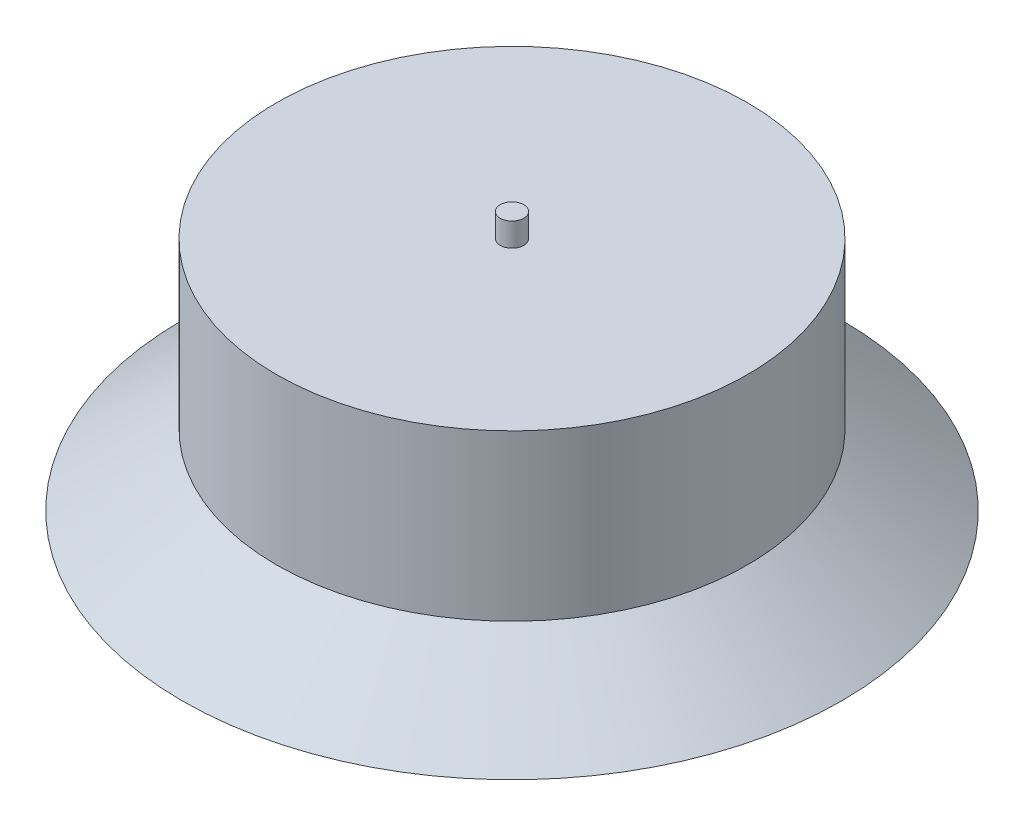
SolidWorks part; units mm, degrees
ref_plane "Front Plane" through (0, 0, 0) normal (0, 0, 1) x (1, 0, 0)
ref_plane "Top Plane" through (0, 0, 0) normal (0, 1, 0) x (1, 0, 0)
ref_plane "Right Plane" through (0, 0, 0) normal (1, 0, 0) x (0, 0, -1)
sketch "Sketch1" plane through (0, 0, 0) normal (0, 1, 0) x (1, 0, 0)
  circle A0 centre (0, 0) radius 100
  dimension "D1" = 200
extrude "Boss-Extrude1" add sketch "Sketch1" along normal blind 100
sketch "Sketch2" plane through (0, 0, 0) normal (1, 0, 0) x (0, 0, -1)
  line L0 (-100, 0) -> (-140, 0)
  line L1 (-100, 0) -> (100, 0) construction
  line L2 (-100, 100) -> (-100, 0) construction
  line L3 (-140, 0) -> (-100, 30)
  line L4 (-100, 30) -> (-100, 0)
  line L5 (0, 0) -> (0, 109.5317) construction
  dimension "D1" = 40
  dimension "D2" = 30
revolve "Revolve1" add sketch "Sketch2" angle 360 about L5
sketch "Sketch3" plane through (0, 100, 0) normal (0, 1, 0) x (1, 0, 0)
  circle A0 centre (0, 0) radius 5
  dimension "D1" = 10
extrude "Boss-Extrude2" add sketch "Sketch3" along normal blind 10
